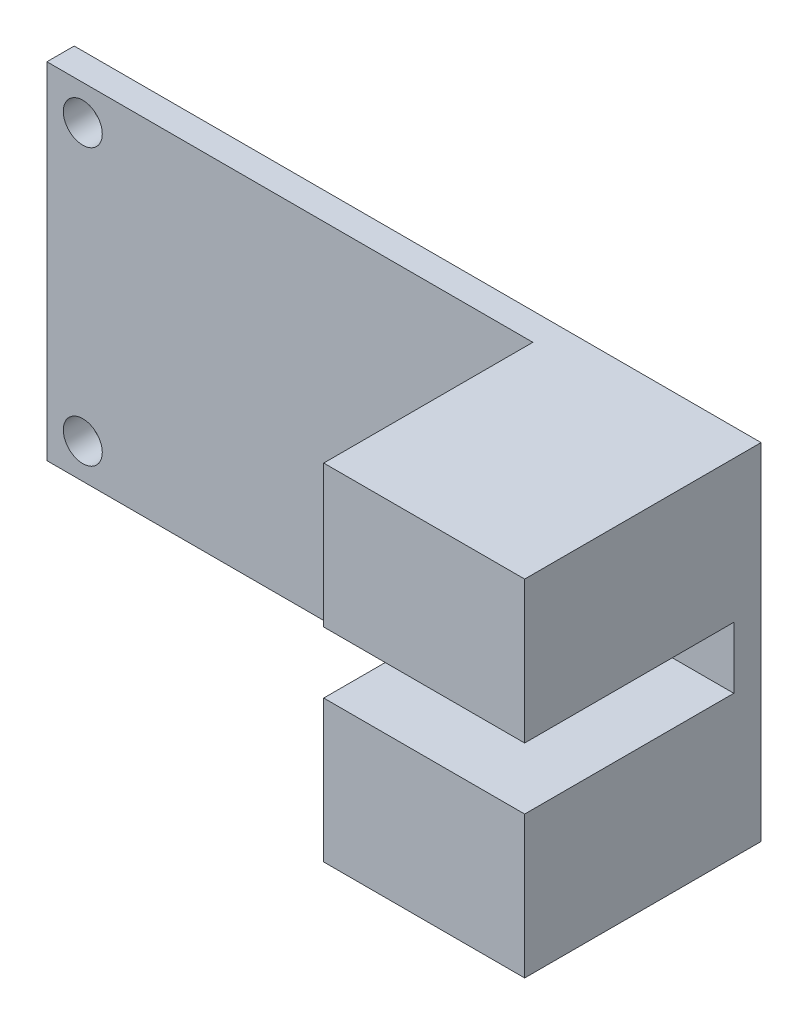
SolidWorks part; units mm, degrees
ref_plane "Front Plane" through (0, 0, 0) normal (0, 0, 1) x (1, 0, 0)
ref_plane "Top Plane" through (0, 0, 0) normal (0, 1, 0) x (1, 0, 0)
ref_plane "Right Plane" through (0, 0, 0) normal (1, 0, 0) x (0, 0, -1)
sketch "Sketch1" plane through (0, 0, 0) normal (0, 0, 1) x (1, 0, 0)
  line L1 (16.75, -8.425) -> (-16.75, -8.425)
  line L2 (16.75, -8.425) -> (16.75, 8.425)
  line L3 (16.75, 8.425) -> (-16.75, 8.425)
  line L4 (-16.75, -8.425) -> (-16.75, 8.425)
  line L5 (16.75, -8.425) -> (-16.75, 8.425) construction
  line L6 (16.75, 8.425) -> (-16.75, -8.425) construction
  circle A0 centre (-15, -6.725) radius 0.95
  circle A1 centre (-15, 6.725) radius 0.95
  point P0 (0, 0)
  point P10 (-16.75, 0)
  point P11 (0, 0)
  dimension "D5" = 1.9
  dimension "D1" = 33.5
  dimension "D2" = 16.85
  dimension "D3" = 13.45
  dimension "D4" = 6.725
  dimension "D6" = 1.75
extrude "Boss-Extrude1" add sketch "Sketch1" along normal blind 1.33
sketch "Sketch2" plane through (0, 0, 1.33) normal (0, 0, 1) x (1, 0, 0)
  line L0 (16.75, -8.425) -> (16.75, 8.425) construction
  line L1 (16.75, 8.425) -> (6.95, 8.425)
  line L2 (16.75, 8.425) -> (16.75, 1.5)
  line L3 (16.75, 1.5) -> (6.95, 1.5)
  line L4 (6.95, 8.425) -> (6.95, 1.5)
  line L5 (16.75, -8.425) -> (6.95, -8.425)
  line L6 (16.75, -8.425) -> (16.75, -1.5)
  line L7 (16.75, -1.5) -> (6.95, -1.5)
  line L8 (6.95, -8.425) -> (6.95, -1.5)
  point P12 (16.75, 0)
  dimension "D1" = 3
  dimension "D2" = 1.5
  dimension "D3" = 9.8
extrude "Boss-Extrude2" add sketch "Sketch2" along normal blind 10.2
equation "\"D4@Sketch1\"=\"D3@Sketch1\"/2"
equation "\"D6@Sketch1\"=0.8+\"D5@Sketch1\"/2"
equation "\"D2@Sketch2\"=\"D1@Sketch2\"/2"
